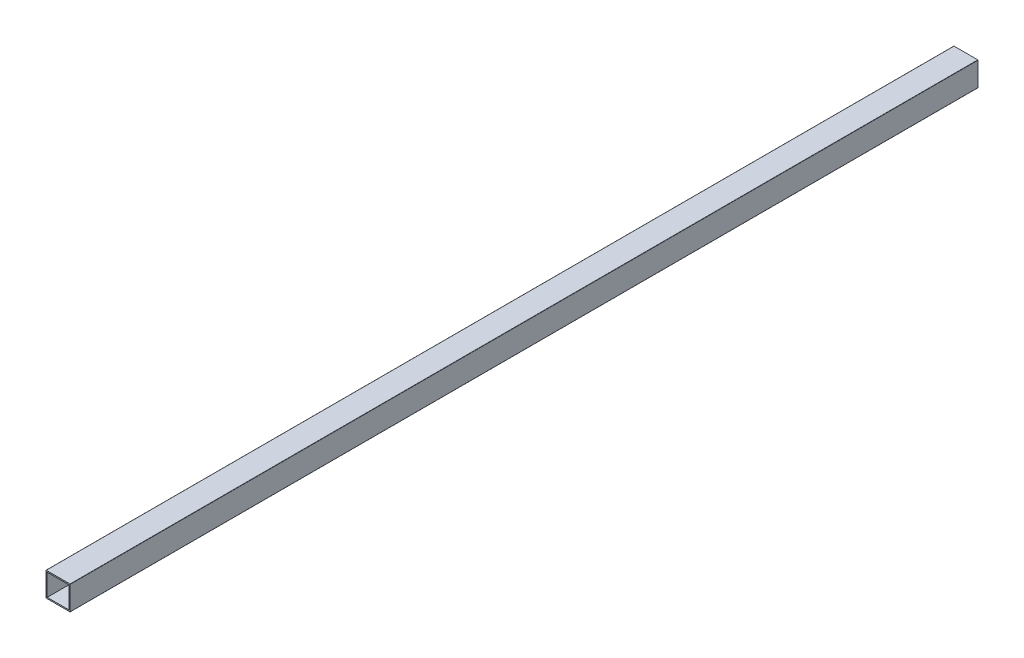
SolidWorks part; units mm, degrees
ref_plane "Front Plane" through (0, 0, 0) normal (0, 0, 1) x (1, 0, 0)
ref_plane "Top Plane" through (0, 0, 0) normal (0, 1, 0) x (1, 0, 0)
ref_plane "Right Plane" through (0, 0, 0) normal (1, 0, 0) x (0, 0, -1)
sketch "Sketch1" plane through (0, 0, 0) normal (0, 0, 1) x (1, 0, 0)
  line L0 (1, 1) -> (19, 1)
  line L1 (0.2, 0) -> (19.8, 0)
  line L2 (0, 0.2) -> (0, 19.8)
  line L3 (0.2, 20) -> (19.8, 20)
  line L4 (20, 0.2) -> (20, 19.8)
  line L5 (19, 1) -> (19, 19)
  line L6 (1, 19) -> (19, 19)
  line L7 (1, 1) -> (1, 19)
  arc A0 (0.2, 0) -> (0, 0.2) centre (0.2, 0.2) cw
  arc A1 (19.8, 0) -> (20, 0.2) centre (19.8, 0.2) ccw
  arc A2 (19.8, 20) -> (20, 19.8) centre (19.8, 19.8) cw
  arc A3 (0, 19.8) -> (0.2, 20) centre (0.2, 19.8) cw
  arc A4 (19, 1) -> (19, 1) centre (19, 1) ccw
  arc A5 (19, 19) -> (19, 19) centre (19, 19) cw
  arc A6 (1, 19) -> (1, 19) centre (1, 19) cw
  arc A7 (1, 1) -> (1, 1) centre (1, 1) cw
  point P7 (0, 0)
  point P10 (20, 0)
  point P13 (20, 20)
  point P16 (0, 20)
  dimension "fillet" = 0.2
  dimension "width" = 20
  dimension "height" = 20
  dimension "thickness" = 1
extrude "Boss-Extrude1" add sketch "Sketch1" along normal blind 750
sketch "Sketch2" plane through (0, 0, 0) normal (-1, 0, 0) x (0, 0, 1)
  line L0 (0, 20) -> (19.7136, 20)
  line L1 (750, 20) -> (0, 20) construction
  line L2 (19.7136, 20) -> (0, 0)
  line L3 (0, 0) -> (0, 20)
  line L18 (750, 0) -> (729.7094, 20)
  line L19 (729.7094, 20) -> (750, 20)
  line L20 (750, 20) -> (750, 0)
  dimension "Skew2" = 90
  dimension "Skew1" = 45.413
extrude "Skew Cut" [suppressed] cut sketch "Sketch2" against normal through all
sketch "Sketch3" plane through (0, 0, 0) normal (-1, 0, 0) x (0, 0, 1)
  line L0 (11.547, 20) -> (0, 0)
  line L2 (750, 20) -> (0, 20) construction
  line L3 (0, 0) -> (0, 20)
  line L4 (0, 20) -> (11.547, 20)
  dimension "Skew3" = 30
extrude "Cut-Extrude2" [suppressed] cut sketch "Sketch3" against normal through all
sketch "Sketch4" plane through (0, 0, 0) normal (-1, 0, 0) x (0, 0, 1)
  line L0 (689.441, 10.2) -> (590.25, 10.2) construction
  line L1 (689.441, 3.45) -> (590.25, 3.45)
  line L2 (689.441, 16.95) -> (590.25, 16.95)
  line L3 (0, 19.8) -> (0, 0.2) construction
  line L4 (750, 0) -> (0, 0) construction
  line L6 (209.441, 10.2) -> (110.25, 10.2) construction
  line L8 (209.441, 3.45) -> (110.25, 3.45)
  line L11 (209.441, 16.95) -> (110.25, 16.95)
  arc A0 (689.441, 3.45) -> (689.441, 16.95) centre (689.441, 10.2) ccw
  arc A1 (590.25, 16.95) -> (590.25, 3.45) centre (590.25, 10.2) ccw
  arc A4 (209.441, 3.45) -> (209.441, 16.95) centre (209.441, 10.2) ccw
  arc A5 (110.25, 16.95) -> (110.25, 3.45) centre (110.25, 10.2) ccw
  point P2 (639.8455, 10.2)
  point P9 (0, 0)
  point P14 (159.8455, 10.2)
  dimension "D3" = 6.75
  dimension "D4" = 110.25
  dimension "D1" = 10.2
  dimension "D2" = 99.191
  dimension "D5" = 2
extrude "Cut-Extrude3" [suppressed] cut sketch "Sketch4" against normal blind 10
sketch "Sketch5" plane through (0, 20, 0) normal (0, 1, 0) x (1, 0, 0)
  line L0 (0, -750) -> (0, 0) construction
  line L1 (5.4496, -270.25) -> (15.4496, -270.25)
  line L2 (5.4496, -270.25) -> (5.4496, -331.75)
  line L3 (5.4496, -331.75) -> (15.4496, -331.75)
  line L4 (15.4496, -270.25) -> (15.4496, -331.75)
  line L5 (5.4496, -750.25) -> (15.4496, -750.25)
  line L10 (5.4496, -750.25) -> (5.4496, -811.75)
  line L11 (5.4496, -811.75) -> (15.4496, -811.75)
  line L12 (15.4496, -750.25) -> (15.4496, -811.75)
  point P6 (0, 0)
  point P12 (0, -480)
  dimension "D1" = 5.4496
  dimension "D2" = 10
  dimension "D3" = 61.5
  dimension "D4" = 270.25
  dimension "D5" = 2
extrude "Cut-Extrude4" [suppressed] cut sketch "Sketch5" against normal blind 10
sketch "Sketch6" [suppressed] plane through (20, 0, 0) normal (1, 0, 0) x (0, 0, -1)
  line L0 (-35, 0.2) -> (-35, 19.8) construction
  circle A0 centre (105, 10) radius 2.5
  circle A1 centre (-15, 10) radius 2.5
  dimension "D2" = 160
  dimension "D3" = 5
  dimension "D1" = 20
extrude "Cut-Extrude5" [suppressed] cut sketch "Sketch6" against normal through all
sketch "Sketch7" [suppressed] plane through (0, 10, 0) normal (0, 1, 0) x (1, 0, 0)
  line L0 (0.2, -110) -> (9.8, -110) construction
  line L1 (0.2, -220) -> (0.2, 0) construction
  line L2 (9.8, -220) -> (9.8, 0) construction
  line L3 (9.8, 0) -> (0.2, 0) construction
  circle A0 centre (5, -50) radius 2.15
  circle A1 centre (5, -170) radius 2.15
  point P9 (5, -110)
  point P14 (5, 0)
  dimension "D1" = 4.3
  dimension "D2" = 60
extrude "Cut-Extrude6" [suppressed] cut sketch "Sketch7" against normal through all
sketch "Sketch8" [suppressed] plane through (0, 0, 0) normal (0, -1, 0) x (1, 0, 0)
  line L0 (0.2, 210) -> (9.8, 210) construction
  circle A0 centre (5, 170) radius 2.15
  circle A1 centre (5, 45) radius 2.15
  point P6 (5, 210)
  dimension "D1" = 4.3
  dimension "D2" = 40
  dimension "D3" = 125
extrude "Cut-Extrude7" [suppressed] cut sketch "Sketch8" against normal through all
